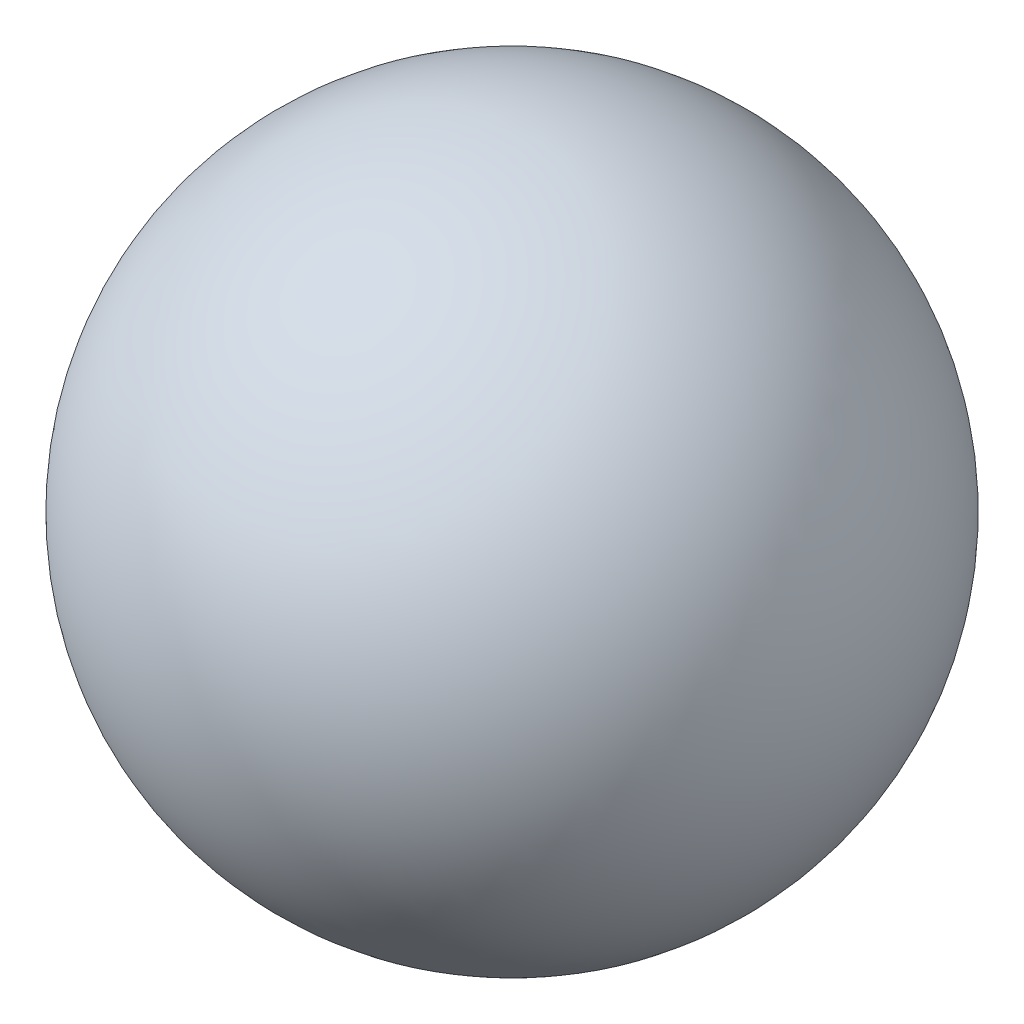
SolidWorks part; units mm, degrees
ref_plane "Front Plane" through (0, 0, 0) normal (0, 0, 1) x (1, 0, 0)
ref_plane "Top Plane" through (0, 0, 0) normal (0, 1, 0) x (1, 0, 0)
ref_plane "Right Plane" through (0, 0, 0) normal (1, 0, 0) x (0, 0, -1)
sketch "Sketch1" plane through (0, 0, 0) normal (0, 0, 1) x (1, 0, 0)
  line L0 (0, 105.0842) -> (0, -101.9811) construction
  line L1 (0, 33.5) -> (0, 28.75)
  line L2 (0, -28.75) -> (0, -33.5)
  line L3 (0, 28.75) -> (0, -28.75)
  arc A0 (0, 33.5) -> (0, -33.5) centre (0, 0) ccw
  dimension "D1" = 33.5
revolve "Revolve1" add sketch "Sketch1" angle 360 about L0
